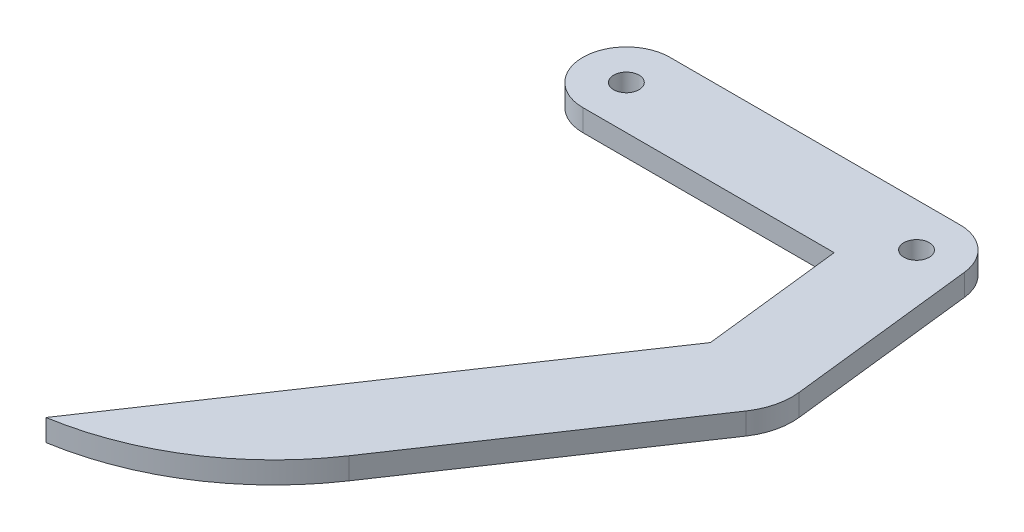
SolidWorks part; units mm, degrees
ref_plane "前基準面" through (0, 0, 0) normal (0, 0, 1) x (1, 0, 0)
ref_plane "上基準面" through (0, 0, 0) normal (0, 1, 0) x (1, 0, 0)
ref_plane "右基準面" through (0, 0, 0) normal (1, 0, 0) x (0, 0, -1)
sketch "草圖1" plane through (0, 0, 0) normal (0, 1, 0) x (1, 0, 0)
  line L1 (-31.0324, 0) -> (31.0324, 0) construction
  line L2 (0, 6) -> (40, 6)
  line L3 (0, -6) -> (34.6468, -6)
  line L5 (45.9612, 0.6814) -> (48.9078, -25.095)
  line L6 (34.6468, -6) -> (36.8486, -25.2606)
  line L8 (47.4762, -30.962) -> (25.446, -63.6883)
  line L9 (36.8486, -25.2606) -> (0, -80)
  arc A0 (0, 6) -> (0, -6) centre (0, 0) ccw
  arc A1 (45.9612, 0.6814) -> (40, 6) centre (40, 0) ccw
  arc A2 (45.9612, 0.6814) -> (40, 6) centre (40, 0) ccw
  arc A3 (47.4762, -30.962) -> (48.9078, -25.095) centre (40.2337, -26.0866) ccw
  arc A4 (47.4762, -30.962) -> (48.9078, -25.095) centre (40.2337, -26.0866) ccw
  arc A6 (0, -80) -> (25.446, -63.6883) centre (-6.1313, -42.4316) ccw
  circle A7 centre (0, 0) radius 1.75
  circle A8 centre (40, 0) radius 1.75
  point P9 (-6, 0)
  point P12 (36.8486, -26.0866)
  point P15 (47.4762, -30.962)
  point P16 (0, 0)
  point P17 (0, 0)
  point P18 (-10.0062, -36.6053)
  point P19 (36.8486, -26.0866)
  point P22 (0, -80)
  point P24 (47.4762, -30.962)
  point P25 (0, -80)
  point P26 (0, -80)
  point P27 (26.9367, -61.4739)
  point P28 (36.8486, -26.0866)
  point P29 (36.8486, -25.095)
  point P30 (0, -80)
  point P31 (40, -26.0866)
  point P32 (40, -26.0866)
  point P33 (36.8486, -25.095)
  point P34 (48.9078, -25.2606)
  point P35 (-10.0062, -36.6053)
  point P36 (-10.0062, -36.6053)
  point P37 (24.9614, -64.4082)
  point P40 (0, -80)
  point P41 (36.8486, -26.0866)
  point P42 (47.4762, -30.962)
  point P43 (25.446, -63.6883)
  dimension "D4" = 6
  dimension "D10" = 38.0654
  dimension "D11" = 3.5
  dimension "D12" = 3.5
  dimension "D9" = 139.532
  dimension "D1" = 40
  dimension "D2" = 12
  dimension "D3" = 12
  dimension "D5" = 12
  dimension "D6" = 80
  dimension "D7" = 25.9443
  dimension "D8" = 96.521
extrude "填料-伸長1" add sketch "草圖1" along normal blind 3 contours L9 A6 L8 A3 L5 A1 L2 A0 L3 L6 A8 A7
